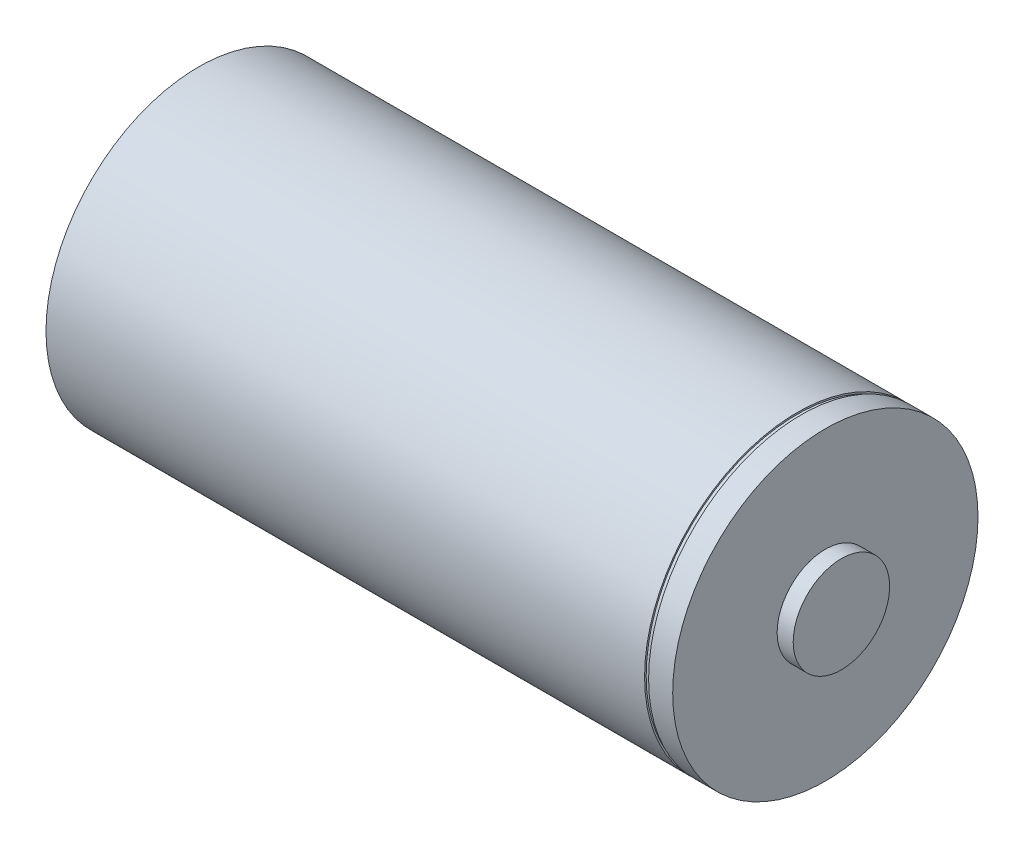
SolidWorks part; units mm, degrees
ref_plane "Ebene vorne" through (0, 0, 0) normal (0, 0, 1) x (1, 0, 0)
ref_plane "Ebene oben" through (0, 0, 0) normal (0, 1, 0) x (1, 0, 0)
ref_plane "Ebene rechts" through (0, 0, 0) normal (1, 0, 0) x (0, 0, -1)
sketch "Skizze1" plane through (0, 0, 0) normal (0, 0, 1) x (1, 0, 0)
  line L0 (0, 0) -> (96.7145, 0) construction
  line L1 (0, 0) -> (0, 19)
  line L2 (0, 19) -> (78, 19)
  line L3 (78, 19) -> (78, 6)
  line L4 (78, 6) -> (80, 6)
  line L5 (80, 6) -> (80, 0)
  line L6 (80, 0) -> (0, 0)
  dimension "D1" = 38
  dimension "D2" = 12
  dimension "D3" = 2
  dimension "D4" = 78
revolve "Rotation1" add sketch "Skizze1" angle 360 about L0
sketch "Skizze2" plane through (0, 0, 0) normal (0, 0, 1) x (1, 0, 0)
  line L0 (0, 0) -> (10.9366, 0) construction
  line L1 (78, 19) -> (0, 19) construction
  line L2 (74.5, 19) -> (75, 19)
  line L3 (74.5, 19) -> (74.5, 18.8)
  line L4 (74.5, 18.8) -> (75, 18.8)
  line L5 (75, 19) -> (75, 18.8)
  line L6 (78, -19) -> (78, 19) construction
  dimension "D1" = 3
  dimension "D2" = 0.5
  dimension "D3" = 0.2
revolve "Schnitt-Rotation1" cut sketch "Skizze2" angle 360 about L0
